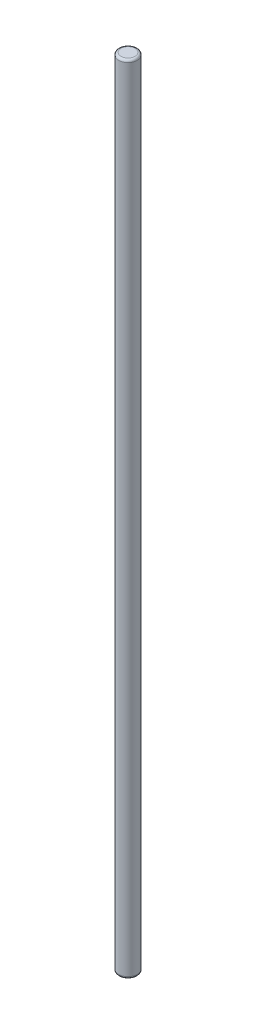
SolidWorks part; units mm, degrees
material "Chrome Stainless Steel"
ref_plane "Front Plane" through (0, 0, 0) normal (0, 0, 1) x (1, 0, 0)
ref_plane "Top Plane" through (0, 0, 0) normal (0, 1, 0) x (1, 0, 0)
ref_plane "Right Plane" through (0, 0, 0) normal (1, 0, 0) x (0, 0, -1)
sketch "Sketch1" plane through (0, 0, 0) normal (0, 1, 0) x (1, 0, 0)
  circle A0 centre (0, 0) radius 4
extrude "Boss-Extrude1" add sketch "Sketch1" along normal blind 342
fillet "Fillet2" radius 1 2 edges at (0, 0, 4) (0, 342, 4)
